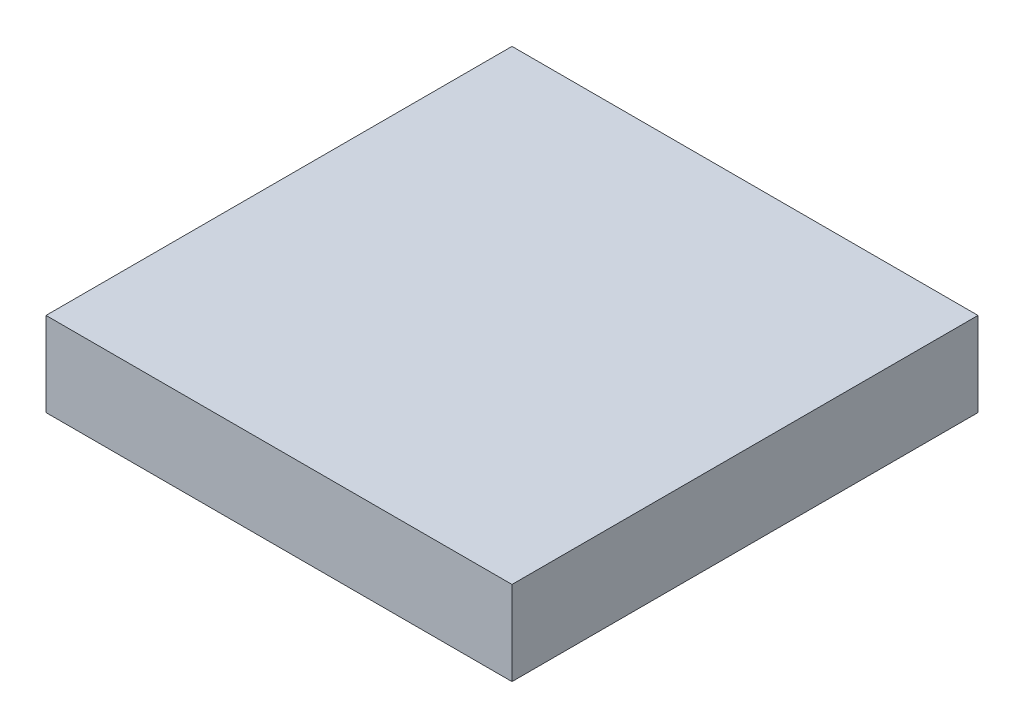
SolidWorks part; units mm, degrees
ref_plane "Alzado" through (0, 0, 0) normal (0, 0, 1) x (1, 0, 0)
ref_plane "Planta" through (0, 0, 0) normal (0, 1, 0) x (1, 0, 0)
ref_plane "Vista lateral" through (0, 0, 0) normal (1, 0, 0) x (0, 0, -1)
sketch "Croquis1" plane through (0, 0, 0) normal (0, 0, 1) x (1, 0, 0)
  line L0 (-51.9597, 8.9278) -> (-51.9597, 3.1482)
  line L1 (-51.9597, 8.9278) -> (-19.9597, 8.9278)
  line L2 (-19.9597, 8.9278) -> (-19.9597, 3.1482)
  line L3 (-19.9597, 3.1482) -> (-35.9597, -4.2902)
  line L4 (-35.9597, -4.2902) -> (-51.9597, 3.1482)
extrude "Saliente-Extruir1" add sketch "Croquis1" along normal blind 32
sketch "Croquis2" plane through (-19.9597, 0, 0) normal (1, 0, 0) x (0, 0, -1)
  line L5 (-32, 8.9278) -> (-32, 3.1482)
  line L6 (-32, 3.1482) -> (-16, -4.2902)
  line L7 (-32, -4.2902) -> (0, -4.2902) construction
  line L8 (-16, -4.2902) -> (-32, -4.2902)
  line L9 (-32, -4.2902) -> (-32, 3.1482)
  line L10 (-16, -4.2902) -> (0, 3.1482)
  line L11 (0, 3.1482) -> (0, -4.2902)
  line L12 (0, -4.2902) -> (-16, -4.2902)
extrude "Cortar-Extruir1" cut sketch "Croquis2" against normal blind 33 contours L12 L11 L10 | L9 L8 L6
sketch "Croquis16" plane through (0, -9.6442, 4.4836) normal (0, -0.9068, 0.4216) x (-1, 0, 0)
  line L0 (35.9597, -12.7001) -> (19.9597, -30.3447) construction
  line L1 (51.9597, -30.3447) -> (35.9597, -12.7001) construction
  line L2 (47.5683, -29.9816) -> (36.0718, -29.9816)
  line L3 (36.0718, -29.9816) -> (24.351, -29.9816)
  arc A0 (47.5683, -29.9816) -> (24.351, -29.9816) centre (35.9597, -29.9816) ccw
extrude "Saliente-Extruir12" add sketch "Croquis16" along normal blind 0.01
sketch "Croquis17" plane through (-8.0308, -17.2743, 0) normal (-0.4216, -0.9068, 0) x (-0.9068, 0.4216, 0)
  line L1 (40.2829, -24.5995) -> (30.7995, -16) construction
  line L2 (30.7995, -16) -> (48.444, 0) construction
  line L3 (48.0807, -16) -> (48.0807, -27.6085)
  line L4 (48.0807, -16) -> (48.0807, -4.3915)
  arc A0 (48.0807, -4.3915) -> (48.0807, -27.6085) centre (48.0807, -16) ccw
extrude "Saliente-Extruir13" add sketch "Croquis17" along normal blind 0.01
sketch "Croquis18" plane through (0, 2.5887, 1.2035) normal (0, -0.9068, -0.4216) x (-1, 0, 0)
  line L0 (35.9597, -16.3174) -> (44.5591, -6.8341) construction
  line L1 (19.9597, 1.3272) -> (35.9597, -16.3174) construction
  line L2 (35.9597, 0.9622) -> (24.3523, 0.9622)
  line L3 (24.3523, 0.9622) -> (47.5671, 0.9622)
  arc A0 (24.3523, 0.9622) -> (47.5671, 0.9622) centre (35.9597, 0.9622) ccw
extrude "Saliente-Extruir14" add sketch "Croquis18" along normal blind 0.01 contours L2 A0 L3
sketch "Croquis19" plane through (-4.7507, 10.2188, 0) normal (0.4216, -0.9068, 0) x (-0.9068, -0.4216, 0)
  line L0 (24.9343, -7.4014) -> (34.4167, -16) construction
  line L1 (34.4167, -16) -> (24.9333, -24.5995) construction
  line L2 (17.143, -16) -> (17.143, -27.6035)
  line L3 (17.143, -27.6035) -> (17.143, -4.3965)
  arc A0 (17.143, -27.6035) -> (17.143, -4.3965) centre (17.143, -16) ccw
extrude "Saliente-Extruir15" add sketch "Croquis19" along normal blind 0.01 contours L2 A0 L3
